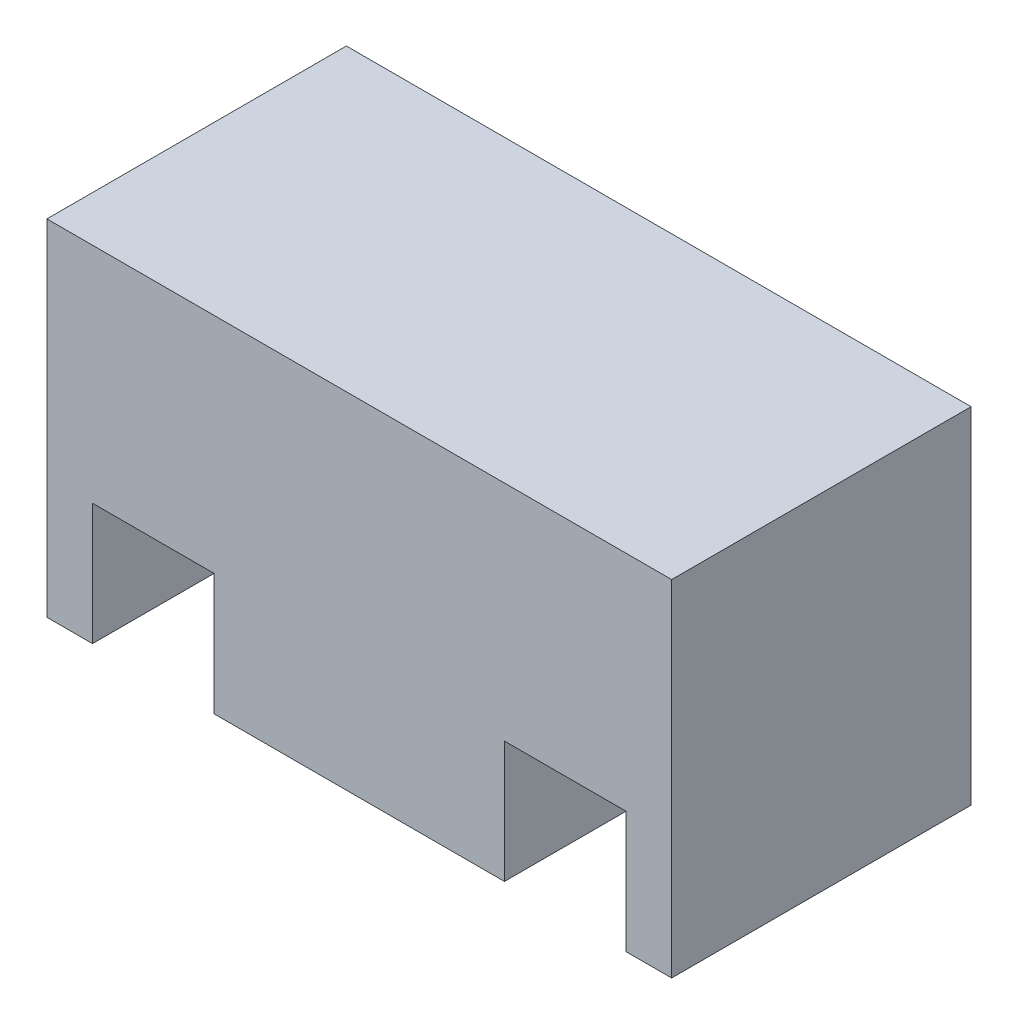
SolidWorks part; units mm, degrees
ref_plane "Front Plane" through (0, 0, 0) normal (0, 0, 1) x (1, 0, 0)
ref_plane "Top Plane" through (0, 0, 0) normal (0, 1, 0) x (1, 0, 0)
ref_plane "Right Plane" through (0, 0, 0) normal (1, 0, 0) x (0, 0, -1)
sketch "Sketch1" plane through (0, 0, 0) normal (0, 0, 1) x (1, 0, 0)
  line L1 (-20.4165, 13.2152) -> (20.6835, 13.2152)
  line L2 (-20.4165, 13.2152) -> (-20.4165, -9.4848)
  line L3 (-20.4165, -9.4848) -> (20.6835, -9.4848)
  line L4 (20.6835, 13.2152) -> (20.6835, -9.4848)
extrude "Boss-Extrude1" add sketch "Sketch1" along normal blind 19.7
sketch "Sketch2" plane through (0, 0, 19.7) normal (0, 0, 1) x (1, 0, 0)
  line L0 (-20.4165, -9.4848) -> (20.6835, -9.4848) construction
  line L1 (-17.4165, -9.4848) -> (-9.4165, -9.4848)
  line L2 (-17.4165, -9.4848) -> (-17.4165, -1.4848)
  line L3 (-17.4165, -1.4848) -> (-9.4165, -1.4848)
  line L4 (-9.4165, -9.4848) -> (-9.4165, -1.4848)
  line L5 (-20.4165, 13.2152) -> (-20.4165, -9.4848) construction
  line L6 (20.6835, -9.4848) -> (20.6835, 13.2152) construction
  line L7 (9.6835, -9.4848) -> (17.6835, -9.4848)
  line L8 (9.6835, -9.4848) -> (9.6835, -1.4848)
  line L9 (9.6835, -1.4848) -> (17.6835, -1.4848)
  line L10 (17.6835, -9.4848) -> (17.6835, -1.4848)
  dimension "D1" = 3
  dimension "D2" = 8
  dimension "D3" = 8
  dimension "D4" = 3
  dimension "D5" = 8
  dimension "D6" = 8
extrude "Cut-Extrude1" cut sketch "Sketch2" against normal through all
